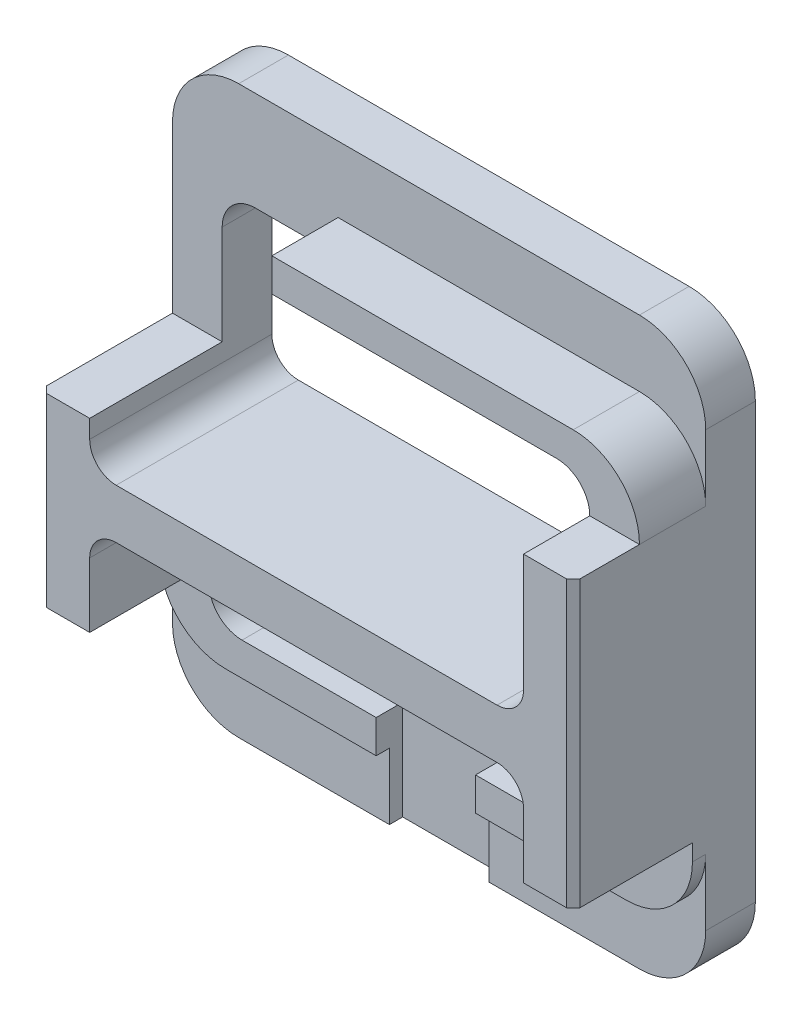
SolidWorks part; units mm, degrees
ref_plane "Front Plane" through (0, 0, 0) normal (0, 0, 1) x (1, 0, 0)
ref_plane "Top Plane" through (0, 0, 0) normal (0, 1, 0) x (1, 0, 0)
ref_plane "Right Plane" through (0, 0, 0) normal (1, 0, 0) x (0, 0, -1)
sketch "Sketch1" plane through (0, 0, 0) normal (0, 0, 1) x (1, 0, 0)
  line L0 (-80.5, 65.5) -> (80.5, -65.5) construction
  line L1 (-60.5, 65.5) -> (60.5, 65.5)
  line L2 (-80.5, 45.5) -> (-80.5, -45.5)
  line L3 (-60.5, -65.5) -> (60.5, -65.5)
  line L4 (80.5, 45.5) -> (80.5, -45.5)
  line L5 (-65.5, 45.5) -> (-65.5, -45.5)
  line L6 (-55.5, -55.5) -> (55.5, -55.5)
  line L7 (65.5, -45.5) -> (65.5, 45.5)
  line L8 (55.5, 55.5) -> (-55.5, 55.5)
  arc A0 (-60.5, 65.5) -> (-80.5, 45.5) centre (-60.5, 45.5) ccw
  arc A1 (-80.5, -45.5) -> (-60.5, -65.5) centre (-60.5, -45.5) ccw
  arc A2 (60.5, -65.5) -> (80.5, -45.5) centre (60.5, -45.5) ccw
  arc A3 (60.5, 65.5) -> (80.5, 45.5) centre (60.5, 45.5) cw
  arc A4 (-65.5, -45.5) -> (-55.5, -55.5) centre (-55.5, -45.5) ccw
  arc A5 (55.5, -55.5) -> (65.5, -45.5) centre (55.5, -45.5) ccw
  arc A6 (65.5, 45.5) -> (55.5, 55.5) centre (55.5, 45.5) ccw
  arc A7 (-65.5, 45.5) -> (-55.5, 55.5) centre (-55.5, 45.5) cw
  point P14 (-80.5, -65.5)
  point P20 (80.5, 65.5)
  point P25 (65.5, -55.5)
  point P30 (-68.1993, 55.4914)
  dimension "D5" = 20
  dimension "D6" = 10
  dimension "D1" = 161
  dimension "D2" = 131
  dimension "D3" = 10
  dimension "D4" = 15
  dimension "D7" = 10
  dimension "D8" = 15
extrude "Boss-Extrude1" add sketch "Sketch1" along normal blind 55
sketch "Sketch3" plane through (0, 0, 0) normal (0, 0, -1) x (-1, 0, 0)
  line L0 (-80.5, 45.5) -> (-80.5, 65.5)
  line L1 (-60.5, 85.5) -> (60.5, 85.5)
  line L2 (80.5, 65.5) -> (80.5, 45.5)
  line L3 (80.5, -45.5) -> (80.5, -65.5)
  line L4 (60.5, -85.5) -> (-60.5, -85.5)
  line L5 (-80.5, -65.5) -> (-80.5, -45.5)
  line L6 (-60.5, 65.5) -> (60.5, 65.5) construction
  line L7 (60.5, -65.5) -> (-60.5, -65.5) construction
  line L8 (-60.5, 65.5) -> (60.5, 65.5)
  line L9 (60.5, -65.5) -> (-60.5, -65.5)
  arc A0 (-60.5, 65.5) -> (-80.5, 45.5) centre (-60.5, 45.5) ccw construction
  arc A1 (80.5, 45.5) -> (60.5, 65.5) centre (60.5, 45.5) ccw construction
  arc A2 (60.5, -65.5) -> (80.5, -45.5) centre (60.5, -45.5) ccw construction
  arc A3 (-80.5, -45.5) -> (-60.5, -65.5) centre (-60.5, -45.5) ccw construction
  arc A4 (-60.5, 65.5) -> (-80.5, 45.5) centre (-60.5, 45.5) ccw
  arc A5 (80.5, 45.5) -> (60.5, 65.5) centre (60.5, 45.5) ccw
  arc A6 (60.5, -65.5) -> (80.5, -45.5) centre (60.5, -45.5) ccw
  arc A7 (-80.5, -45.5) -> (-60.5, -65.5) centre (-60.5, -45.5) ccw
  arc A8 (-60.5, -85.5) -> (-80.5, -65.5) centre (-60.5, -65.5) cw
  arc A9 (80.5, -65.5) -> (60.5, -85.5) centre (60.5, -65.5) cw
  arc A10 (60.5, 85.5) -> (80.5, 65.5) centre (60.5, 65.5) cw
  arc A11 (-80.5, 65.5) -> (-60.5, 85.5) centre (-60.5, 65.5) cw
  dimension "D3" = 20
  dimension "D1" = 20
  dimension "D2" = 20
extrude "Boss-Extrude3" add sketch "Sketch3" against normal blind 15
sketch "Sketch4" plane through (0, 0, 55) normal (0, 0, 1) x (1, 0, 0)
  line L1 (-95.2327, -40.5) -> (94.7808, -40.5)
  line L2 (-95.2327, -40.5) -> (-95.2327, -65.5)
  line L3 (-95.2327, -65.5) -> (94.7808, -65.5)
  line L4 (94.7808, -40.5) -> (94.7808, -65.5)
  dimension "D1" = 25
extrude "Cut-Extrude1" cut sketch "Sketch4" against normal offset from surface (36 mm away) 4 up to face at (0, -67.5711, 15)
sketch "Sketch5" plane through (0, 0, 19) normal (0, 0, 1) x (1, 0, 0)
  line L0 (55.5, -55.5) -> (-55.5, -55.5) construction
  line L1 (-15, -55.5) -> (15, -55.5)
  line L2 (-15, -55.5) -> (-15, -85.5)
  line L3 (60.5, -85.5) -> (-60.5, -85.5) construction
  line L4 (15, -55.5) -> (15, -85.5)
  line L6 (-15, -85.5) -> (15, -85.5)
  dimension "D1" = 15
  dimension "D2" = 30
extrude "Cut-Extrude2" cut sketch "Sketch5" against normal blind 8
sketch "Sketch6" plane through (0, 0, 55) normal (0, 0, 1) x (1, 0, 0)
  line L0 (60.5, 65.5) -> (-60.5, 65.5) construction
  line L1 (-102.9146, 75.3254) -> (-30.5, 75.3254)
  line L2 (-102.9146, 75.3254) -> (-102.9146, 15.5)
  line L3 (-102.9146, 15.5) -> (-30.5, 15.5)
  line L4 (-30.5, 75.3254) -> (-30.5, 15.5)
  line L5 (-80.5, 45.5) -> (-80.5, -40.5) construction
  dimension "D1" = 50
  dimension "D2" = 50
extrude "Cut-Extrude3" cut sketch "Sketch6" against normal up to surface (40 mm away) up to face at (0, 67.5711, 15)
sketch "Sketch7" plane through (0, 0, 55) normal (0, 0, 1) x (1, 0, 0)
  line L1 (-37.3927, 95.1582) -> (105.8518, 95.1582)
  line L2 (-37.3927, 95.1582) -> (-37.3927, 45.5)
  line L3 (-37.3927, 45.5) -> (105.8518, 45.5)
  line L4 (105.8518, 95.1582) -> (105.8518, 45.5)
extrude "Cut-Extrude4" cut sketch "Sketch7" against normal blind 20
sketch "Sketch8" plane through (0, 0, 0) normal (0, 0, -1) x (-1, 0, 0)
  line L0 (-65.5, -45.5) -> (-65.5, 45.5) construction
  line L1 (-65.5, 2) -> (65.5, 2)
  line L2 (-65.5, 2) -> (-65.5, -13)
  line L3 (-65.5, -13) -> (65.5, -13)
  line L4 (65.5, 2) -> (65.5, -13)
  line L5 (65.5, 45.5) -> (65.5, -45.5) construction
  dimension "D1" = 2
  dimension "D2" = 15
extrude "Boss-Extrude4" add sketch "Sketch8" against normal up to surface (55 mm away) up to face at (-73, -12.5, 55)
fillet "Fillet1" radius 8 4 edges at (-65.5, 2, 27.5) (65.5, 2, 27.5) (65.5, -13, 27.5) (-65.5, -13, 27.5)
chamfer "Chamfer1" distance 2 angle 45 2 edges at (80.5, 2.5, 55) (-80.5, -12.5, 55)
